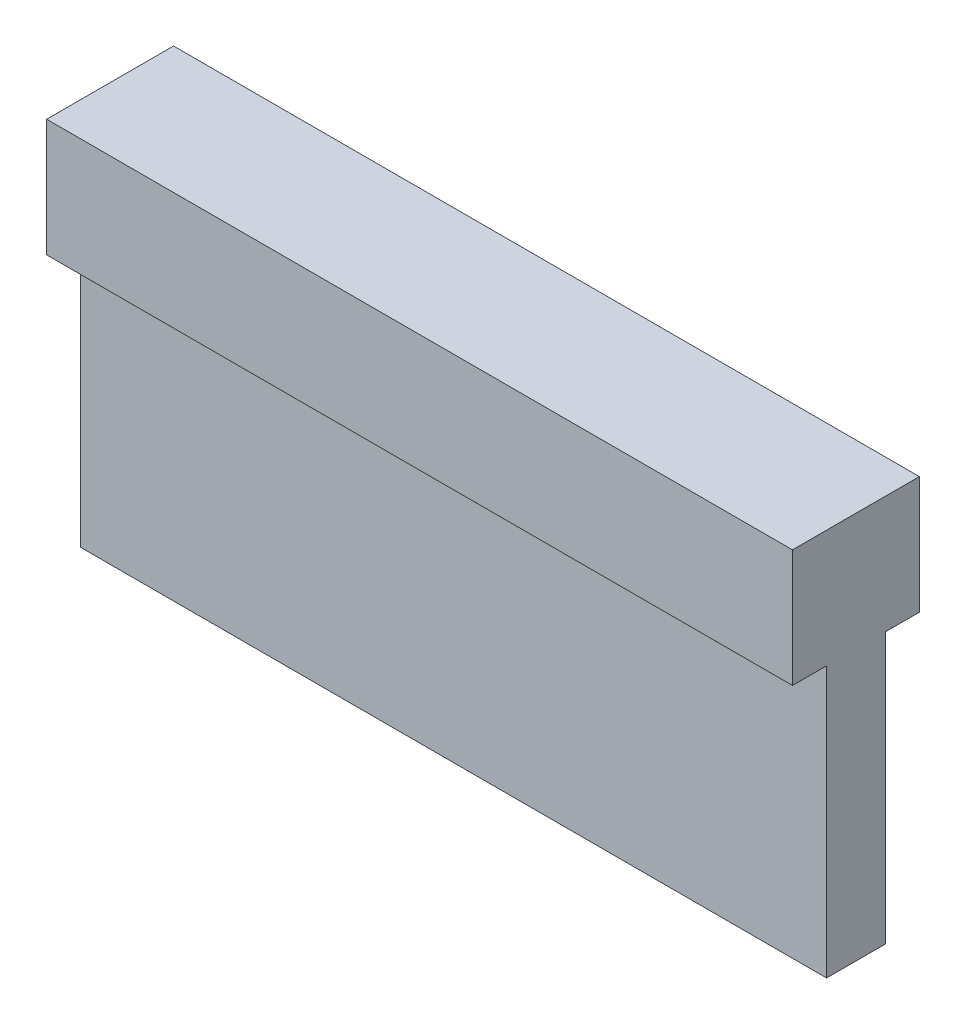
SolidWorks part; units mm, degrees
ref_plane "Front Plane" through (0, 0, 0) normal (0, 0, 1) x (1, 0, 0)
ref_plane "Top Plane" through (0, 0, 0) normal (0, 1, 0) x (1, 0, 0)
ref_plane "Right Plane" through (0, 0, 0) normal (1, 0, 0) x (0, 0, -1)
sketch "Sketch1" plane through (0, 0, 0) normal (1, 0, 0) x (0, 0, -1)
  line L0 (-1.25, -2.5) -> (-1.25, -14.01)
  line L1 (-2.7, 2.5) -> (2.7, 2.5)
  line L2 (-2.7, 2.5) -> (-2.7, -2.5)
  line L3 (-2.7, -2.5) -> (-1.25, -2.5)
  line L4 (2.7, 2.5) -> (2.7, -2.5)
  line L5 (-2.7, 2.5) -> (2.7, -2.5) construction
  line L6 (-2.7, -2.5) -> (2.7, 2.5) construction
  line L7 (-1.25, -14.01) -> (1.25, -14.01)
  line L8 (1.25, -14.01) -> (1.25, -2.5)
  line L9 (-1.25, -8.255) -> (1.25, -8.255) construction
  line L10 (1.25, -2.5) -> (2.7, -2.5)
  point P0 (0, 0)
  point P12 (0, -8.255)
  dimension "D1" = 5.4
  dimension "D2" = 5
  dimension "D3" = 2.5
  dimension "D4" = 16.51
extrude "Boss-Extrude1" add sketch "Sketch1" along normal blind 31.75
